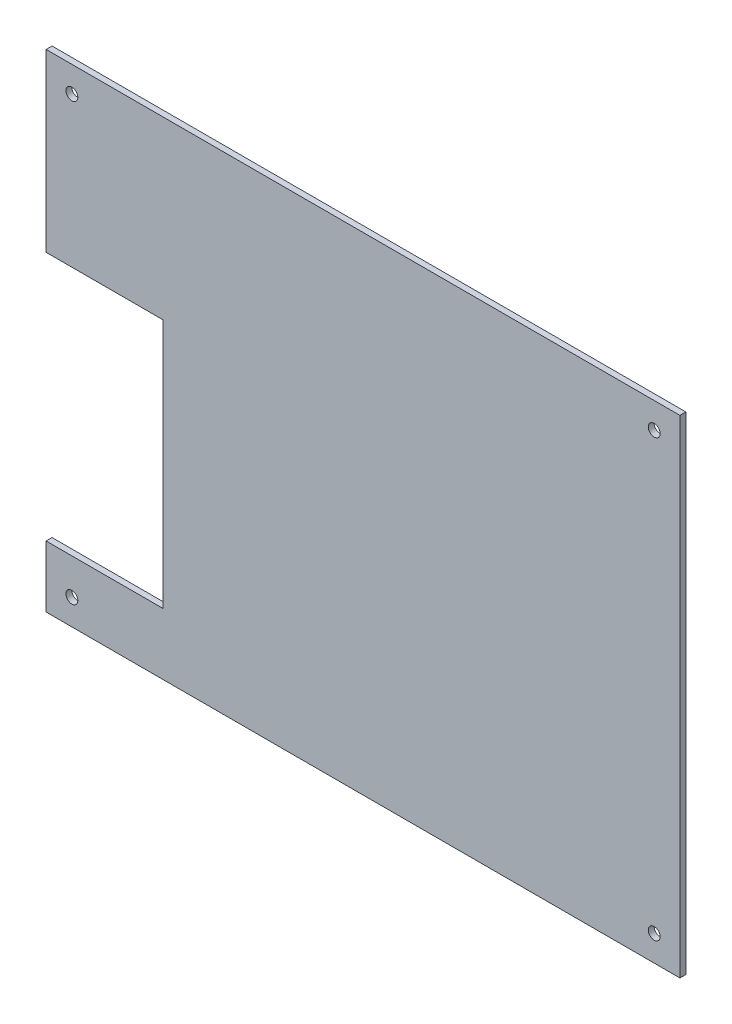
SolidWorks part; units mm, degrees
material "1060 合金"
ref_plane "前视基准面" through (0, 0, 0) normal (0, 0, 1) x (1, 0, 0)
ref_plane "上视基准面" through (0, 0, 0) normal (0, 1, 0) x (1, 0, 0)
ref_plane "右视基准面" through (0, 0, 0) normal (1, 0, 0) x (0, 0, -1)
sketch "草图1" plane through (0, 0, 0) normal (0, 0, 1) x (1, 0, 0)
  line L84 (352.6084, -1072.8029) -> (1952.6084, -1072.8029)
  line L85 (352.6084, -1072.8029) -> (352.6084, -2302.8029)
  line L86 (352.6084, -2302.8029) -> (1952.6084, -2302.8029)
  line L87 (1952.6084, -1072.8029) -> (1952.6084, -2302.8029)
  circle A108 centre (417.6084, -1137.8029) radius 15
  circle A109 centre (1887.6084, -1137.8029) radius 15
  circle A110 centre (1887.6084, -2237.8029) radius 15
  circle A111 centre (417.6084, -2237.8029) radius 15
  dimension "D25" = 1600
  dimension "D90" = 65
  dimension "D91" = 65
  dimension "D92" = 65
  dimension "D93" = 65
  dimension "D94" = 65
  dimension "D95" = 65
  dimension "D96" = 65
  dimension "D97" = 65
  dimension "D48" = 1230
extrude "凸台-拉伸1" add sketch "草图1" along normal blind 3
scale "缩放比例1" bodies to scale 101 104 102 103 108 scale about centroid uniform scaling no x scale factor 0.1 y scale factor 0.1 z scale factor 0.5
sketch "草图2" plane through (0, 0, 2.25) normal (0, 0, 1) x (1, 0, 0)
  line L0 (1072.6084, -1626.3029) -> (1072.6084, -1749.3029) construction
  line L1 (1072.6084, -1670.6629) -> (1102.1084, -1670.6629)
  line L2 (1072.6084, -1670.6629) -> (1072.6084, -1733.7629)
  line L3 (1072.6084, -1733.7629) -> (1102.1084, -1733.7629)
  line L4 (1102.1084, -1670.6629) -> (1102.1084, -1733.7629)
  line L5 (1232.6084, -1626.3029) -> (1072.6084, -1626.3029) construction
  line L6 (1072.6084, -1749.3029) -> (1232.6084, -1749.3029) construction
  dimension "D1" = 63.1
  dimension "D2" = 29.5
  dimension "D3" = 44.36
  dimension "D4" = 15.54
extrude "切除-拉伸1" cut sketch "草图2" against normal through all contours L4 L3 L2 L1
